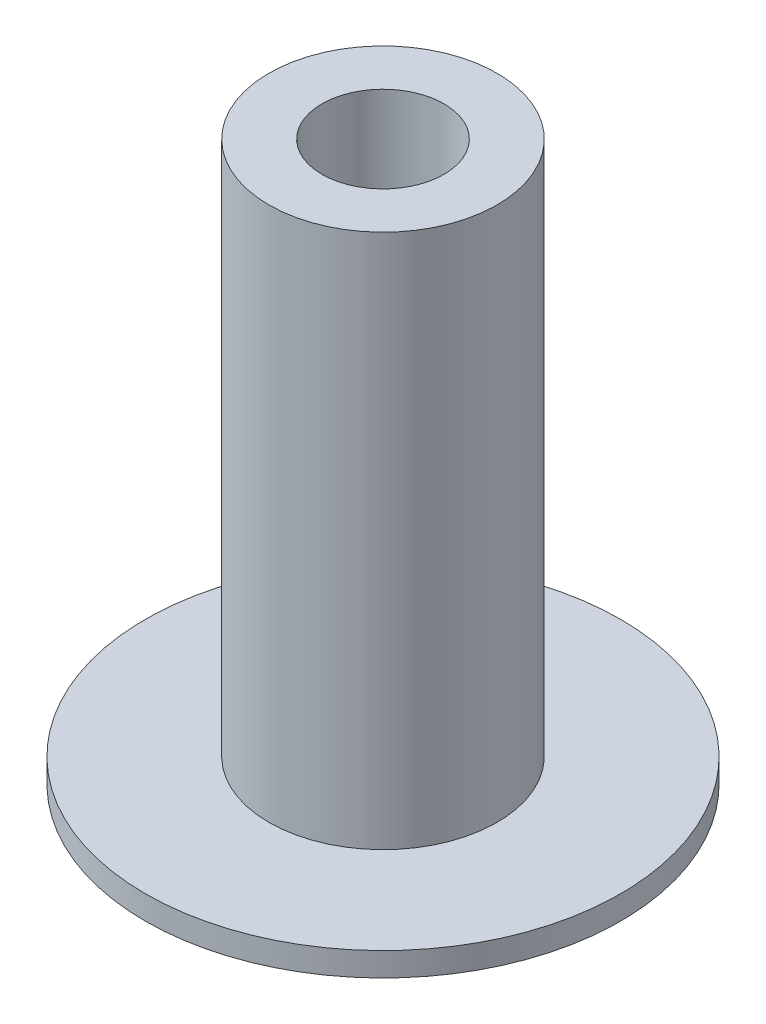
SolidWorks part; units mm, degrees
ref_plane "Front Plane" through (0, 0, 0) normal (0, 0, 1) x (1, 0, 0)
ref_plane "Top Plane" through (0, 0, 0) normal (0, 1, 0) x (1, 0, 0)
ref_plane "Right Plane" through (0, 0, 0) normal (1, 0, 0) x (0, 0, -1)
sketch "Sketch1" plane through (0, 0, 0) normal (0, 1, 0) x (1, 0, 0)
  circle A0 centre (0, 0) radius 12.7
  dimension "D1" = 25.4
extrude "Boss-Extrude1" add sketch "Sketch1" along normal blind 1.27
sketch "Sketch2" plane through (0, 1.27, 0) normal (0, 1, 0) x (1, 0, 0)
  circle A0 centre (0, 0) radius 6.096
  dimension "D1" = 12.192
extrude "Boss-Extrude2" add sketch "Sketch2" along normal blind 28.575
hole_wizard "5/16-18 Tapped Hole1" positions "Sketch3" profile "Sketch5" tap size "5/16-18" standard "ANSI Inch" end condition through all
sketch "Sketch3" plane through (0, 29.845, 0) normal (0, 1, 0) x (1, 0, 0)
  point P0 (0, 0)
cosmetic thread "Hole Thread1"
sketch "Sketch5" plane through (0, 29.845, 0) normal (1, 0, 0) x (0, 0, 1)
  line L0 (0, 0) -> (0, 29.845)
  line L1 (0, 29.845) -> (3.2639, 29.845)
  line L2 (3.2639, 29.845) -> (3.2639, 0)
  line L5 (3.2639, 0) -> (0, 0)
  line L11 (0, -6.35) -> (0, 107.95) construction
  dimension "Thru Tap Drill Dia." = 6.5278
  dimension "Thru Tap Drill Depth" = 29.845
